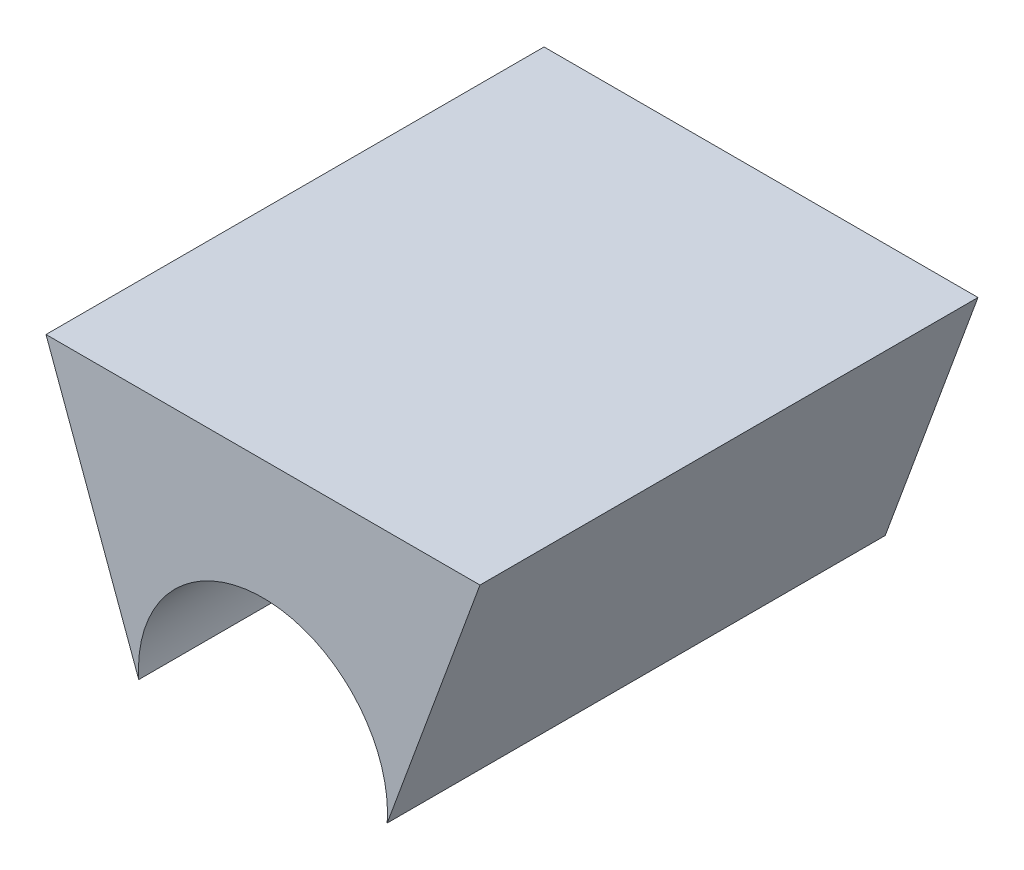
SolidWorks part; units mm, degrees
ref_plane "Front Plane" through (0, 0, 0) normal (0, 0, 1) x (1, 0, 0)
ref_plane "Top Plane" through (0, 0, 0) normal (0, 1, 0) x (1, 0, 0)
ref_plane "Right Plane" through (0, 0, 0) normal (1, 0, 0) x (0, 0, -1)
sketch "Sketch1" plane through (0, 0, 0) normal (0, 0, 1) x (1, 0, 0)
  line L0 (-4.5, 5) -> (4.5, 5) construction
  line L1 (-4.5, 5) -> (-2.3467, -0.862) construction
  line L2 (4.5, 5) -> (2.3467, -0.862) construction
  line L3 (-4.3567, 4.9) -> (-2.2528, -0.8275)
  line L4 (4.3567, 4.9) -> (2.2528, -0.8275)
  line L5 (-4.3567, 4.9) -> (4.3567, 4.9)
  arc A0 (-2.3467, -0.862) -> (2.3467, -0.862) centre (0, 0) ccw construction
  arc A1 (-2.2528, -0.8275) -> (2.2528, -0.8275) centre (0, 0) ccw
  point P5 (0, 5)
  dimension "D3" = 2.5
  dimension "D1" = 9
  dimension "D2" = 5
  dimension "D4" = 0.1
extrude "Boss-Extrude1" add sketch "Sketch1" along normal blind 10
sketch "Sketch2" plane through (0, 0, 10) normal (0, 0, 1) x (1, 0, 0)
  circle A0 centre (0, 0) radius 2.5
  dimension "D1" = 5
extrude "Cut-Extrude1" cut sketch "Sketch2" against normal through all
